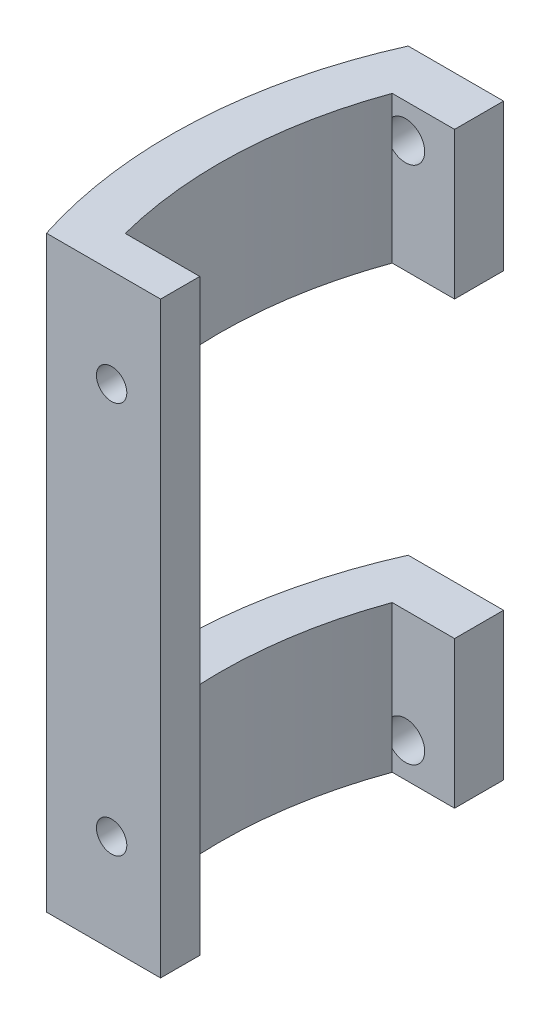
SolidWorks part; units mm, degrees
ref_plane "Front Plane" through (0, 0, 0) normal (0, 0, 1) x (1, 0, 0)
ref_plane "Top Plane" through (0, 0, 0) normal (0, 1, 0) x (1, 0, 0)
ref_plane "Right Plane" through (0, 0, 0) normal (1, 0, 0) x (0, 0, -1)
sketch "Sketch1" plane through (0, 0, 0) normal (0, 1, 0) x (1, 0, 0)
  line L0 (-46.6476, -15) -> (46.6476, -15)
  line L1 (-43.2666, -23) -> (43.2666, -23)
  line L2 (-55, 0) -> (55, 0) construction
  line L3 (-44.7325, 20) -> (44.7325, 20)
  line L4 (-41.3642, 15) -> (46.6476, 15)
  line L5 (-42.6028, -11) -> (47.7493, -11)
  line L6 (-35, 20) -> (-35, -15)
  line L7 (0, -55) -> (0, 55) construction
  circle A0 centre (0, 0) radius 49
  arc A1 (-41.3642, 15) -> (-42.6028, -11) centre (0, 0) ccw
  arc A2 (-41.3642, -15) -> (-39.1918, 20) centre (0, 0) ccw
  dimension "D1" = 98
  dimension "D2" = 88
  dimension "D3" = 8
  dimension "D4" = 15
  dimension "D5" = 35
  dimension "D6" = 5
  dimension "D7" = 4
  dimension "D8" = 35
extrude "Boss-Extrude1" add sketch "Sketch1" along normal blind 60 contours A1 L4 L6 L3 A0 L0 L5
sketch "Sketch2" plane through (0, 0, 11) normal (0, 0, -1) x (-1, 0, 0)
  line L0 (42.6028, 60) -> (35, 60) construction
  circle A0 centre (39.9976, 50) radius 1.55
  circle A1 centre (39.9976, 10) radius 1.55
  dimension "D1" = 6.65
  dimension "D2" = 10
  dimension "D3" = 2
extrude "Cut-Extrude1" cut sketch "Sketch2" against normal through all
sketch "Sketch3" plane through (0, 0, -20) normal (0, 0, -1) x (-1, 0, 0)
  line L0 (0, 19.25) -> (0, -19.25) construction
  line L1 (7.7, 0) -> (-7.7, 0) construction
  circle A0 centre (40, 3.5) radius 1.95
  circle A1 centre (40, 56.5) radius 1.95
  dimension "D1" = 40
  dimension "D2" = 3.5
  dimension "D3" = 2
extrude "Cut-Extrude2" cut sketch "Sketch3" against normal up to surface (5 mm away) up to face at (-38.1821, 30, -15)
sketch "Sketch4" plane through (-35, 0, 0) normal (1, 0, 0) x (0, 0, -1)
  line L0 (20, 45) -> (-11, 45)
  line L2 (20, 60) -> (20, 0) construction
  line L3 (-11, 60) -> (-11, 0) construction
  line L4 (-11, 45) -> (-11, 15)
  line L5 (-11, 15) -> (20, 15)
  line L6 (20, 15) -> (20, 45)
  line L7 (15, 60) -> (-11, 60) construction
  point P8 (20, 30)
  dimension "D1" = 30
  dimension "D2" = 30
extrude "Cut-Extrude3" cut sketch "Sketch4" against normal through all
